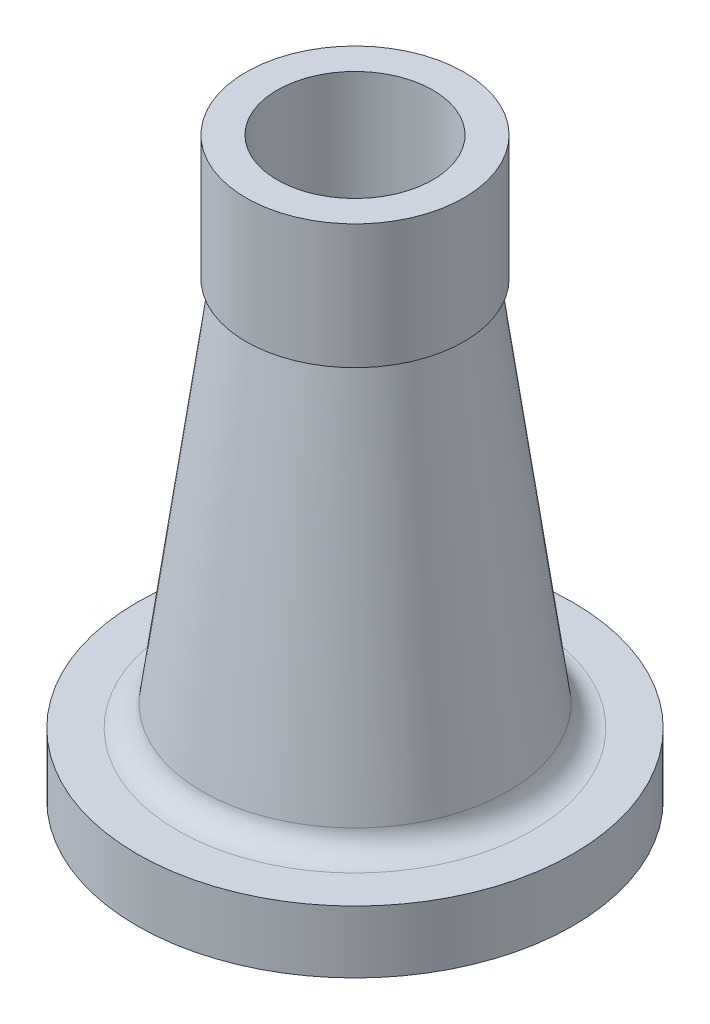
SolidWorks part; units mm, degrees
material "Gray Cast Iron"
ref_plane "Front Plane" through (0, 0, 0) normal (0, 0, 1) x (1, 0, 0)
ref_plane "Top Plane" through (0, 0, 0) normal (0, 1, 0) x (1, 0, 0)
ref_plane "Right Plane" through (0, 0, 0) normal (1, 0, 0) x (0, 0, -1)
sketch "Sketch1" plane through (0, 0, 0) normal (0, 0, 1) x (1, 0, 0)
  line L0 (50, 0) -> (70, 0)
  line L1 (70, 0) -> (70, 20)
  line L2 (70, 20) -> (50, 20)
  line L3 (50, 20) -> (33, 145)
  line L4 (33, 145) -> (35, 145)
  line L5 (35, 145) -> (35, 185)
  line L6 (35, 185) -> (25, 185)
  line L7 (25, 185) -> (25, 129.6172)
  line L8 (25, 129.6172) -> (42.2199, 3)
  line L9 (42.2199, 3) -> (50, 3)
  line L10 (50, 3) -> (50, 0)
  line L11 (0, 0) -> (0, 185) construction
  point P14 (0, 0)
  point P15 (0, 0)
  point P16 (0, 0)
  dimension "D1" = 70
  dimension "D2" = 50
  dimension "D3" = 35
  dimension "D4" = 25
  dimension "D5" = 33
  dimension "D6" = 50
  dimension "D7" = 3
  dimension "D8" = 185
  dimension "D9" = 40
  dimension "D10" = 20
  dimension "D11" = 10
revolve "Revolve1" add sketch "Sketch1" angle 360 about L11
fillet "Fillet1" radius 8 1 edges at (0, 20, -50)
